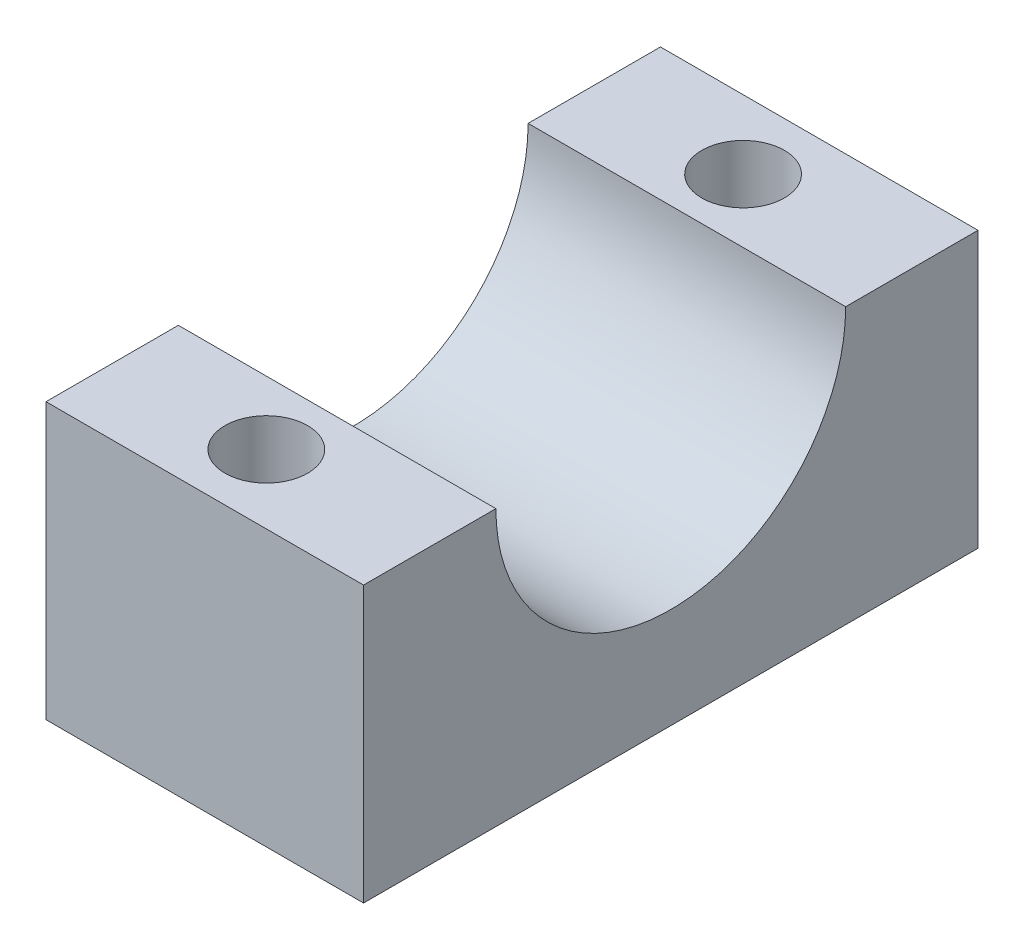
SolidWorks part; units mm, degrees
ref_plane "Front Plane" through (0, 0, 0) normal (0, 0, 1) x (1, 0, 0)
ref_plane "Top Plane" through (0, 0, 0) normal (0, 1, 0) x (1, 0, 0)
ref_plane "Right Plane" through (0, 0, 0) normal (1, 0, 0) x (0, 0, -1)
sketch "Sketch1" plane through (0, 0, 0) normal (1, 0, 0) x (0, 0, -1)
  line L0 (-11.155, 5) -> (-11.155, -5)
  line L1 (-6.155, -5) -> (6.155, -5)
  line L3 (-11.155, 5) -> (11.155, 5)
  line L5 (-11.155, -5) -> (11.155, 5) construction
  line L6 (-11.155, 5) -> (11.155, -5) construction
  line L7 (-11.155, -5) -> (11.155, -5)
  line L8 (11.155, -5) -> (11.155, 5)
  circle A0 centre (0, 5) radius 6.35
  point P0 (0, 0)
  dimension "D2" = 12.7
  dimension "D1" = 22.31
  dimension "D3" = 10
extrude "Boss-Extrude1" add sketch "Sketch1" along normal blind 11.53
sketch "Sketch2" plane through (0, 5, 0) normal (0, 1, 0) x (1, 0, 0)
  line L0 (0, 6.35) -> (0, 11.155) construction
  line L3 (0, -11.155) -> (0, -6.35) construction
  line L4 (11.53, -11.155) -> (0, -11.155) construction
  line L5 (11.53, 11.155) -> (0, 11.155) construction
  circle A0 centre (5.5, -8.655) radius 1.5
  circle A1 centre (5.5, 8.655) radius 1.5
  dimension "D1" = 3
  dimension "D2" = 3
  dimension "D6" = 5.5
  dimension "D4" = 2.5
  dimension "D5" = 2.5
  dimension "D3" = 5.5
extrude "Cut-Extrude1" cut sketch "Sketch2" against normal blind 10
